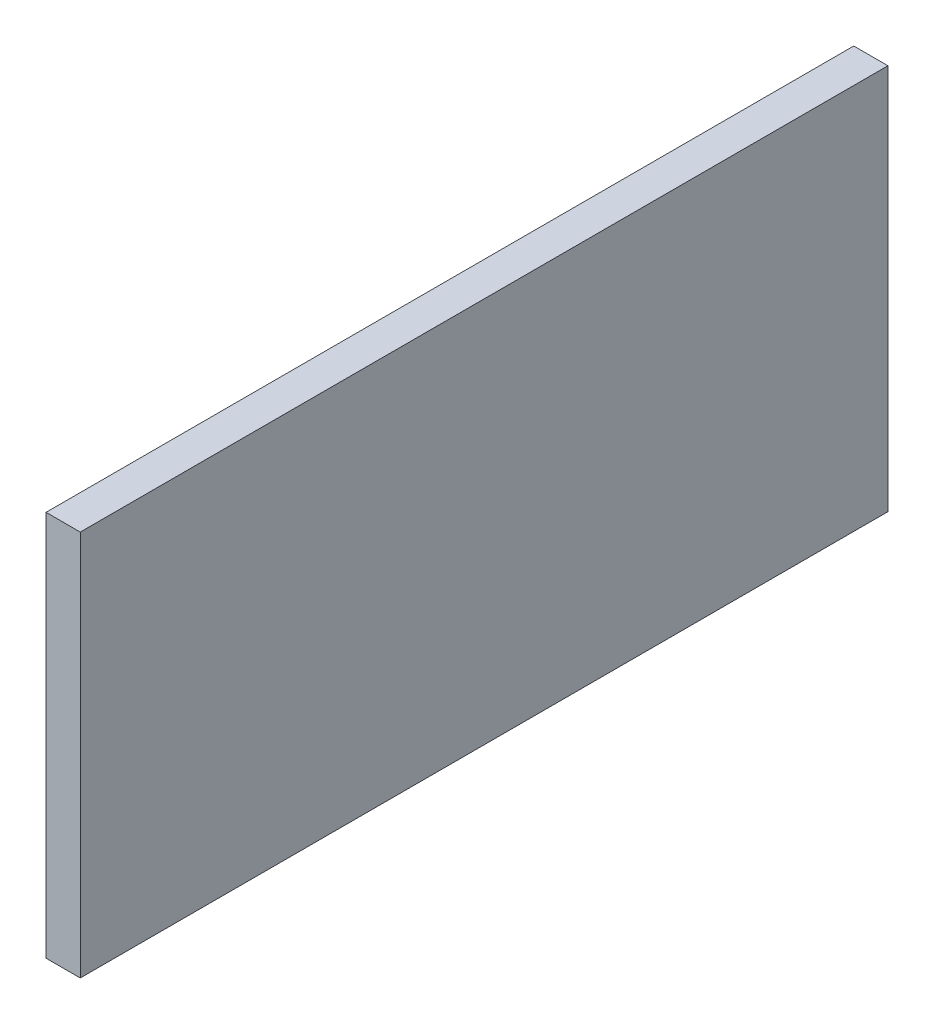
SolidWorks part; units mm, degrees
ref_plane "Front Plane" through (0, 0, 0) normal (0, 0, 1) x (1, 0, 0)
ref_plane "Top Plane" through (0, 0, 0) normal (0, 1, 0) x (1, 0, 0)
ref_plane "Right Plane" through (0, 0, 0) normal (1, 0, 0) x (0, 0, -1)
sketch "Sketch1" plane through (0, 0, 0) normal (1, 0, 0) x (0, 0, -1)
  line L0 (9.3435, -8.5164) -> (6.3435, -8.5164) construction
  line L1 (-64.507, -8.5164) -> (6.3435, -8.5164)
  line L2 (-64.507, -8.5164) -> (-64.507, -42.3934)
  line L3 (-64.507, -42.3934) -> (6.3435, -42.3934)
  line L4 (6.3435, -8.5164) -> (6.3435, -42.3934)
  line L5 (6.3435, -42.3934) -> (-64.507, -42.3934) construction
  point P0 (0, 0)
  point P6 (0, 0)
  point P8 (0, 0)
  point P9 (0, 0)
  point P10 (0, 0)
  point P11 (0, 0)
  point P12 (0, 0)
  point P13 (0, 0)
  point P14 (0, 0)
extrude "Boss-Extrude1" add sketch "Sketch1" along normal blind 3
